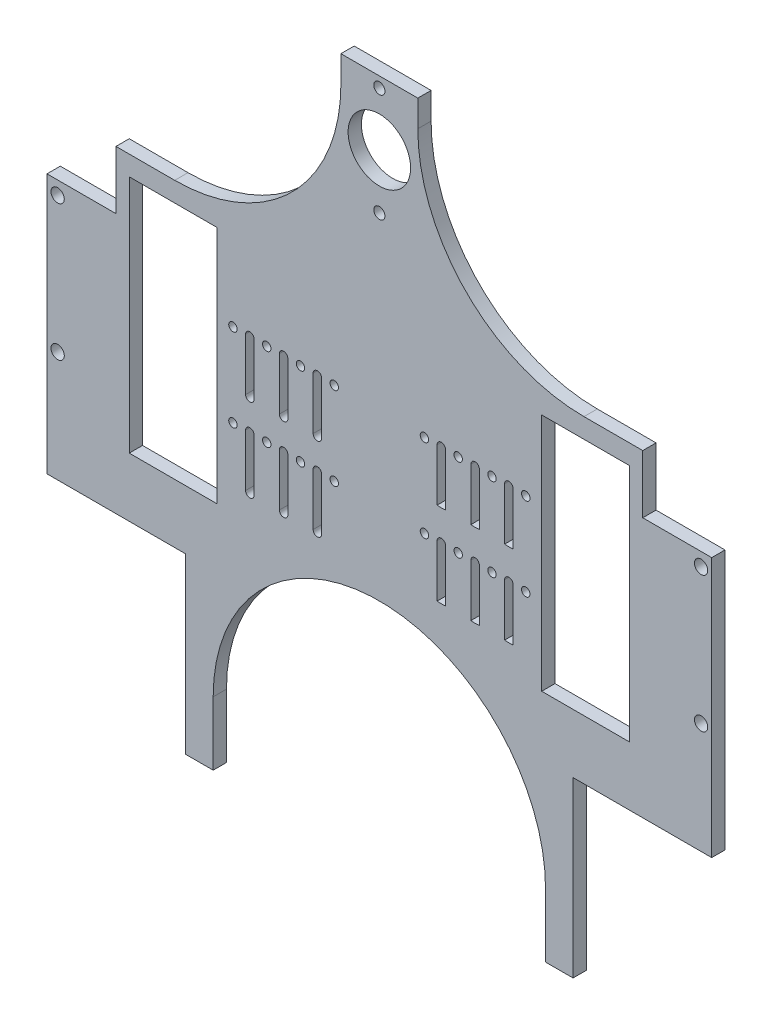
SolidWorks part; units mm, degrees
ref_plane "Front Plane" through (0, 0, 0) normal (0, 0, 1) x (1, 0, 0)
ref_plane "Top Plane" through (0, 0, 0) normal (0, 1, 0) x (1, 0, 0)
ref_plane "Right Plane" through (0, 0, 0) normal (1, 0, 0) x (0, 0, -1)
sketch "Sketch1" plane through (0, 0, 0) normal (0, 0, 1) x (1, 0, 0)
  line L0 (125, 0) -> (125, -340.4) construction
  line L1 (0, 0) -> (250, 0)
  line L2 (0, 0) -> (0, -340.4)
  line L3 (0, -340.4) -> (250, -340.4)
  line L4 (250, 0) -> (250, -340.4)
  line L9 (186.06, -79.9) -> (219.06, -79.9)
  line L10 (186.06, -79.9) -> (186.06, -169.9)
  line L11 (186.06, -169.9) -> (219.06, -169.9)
  line L12 (219.06, -79.9) -> (219.06, -169.9)
  line L13 (180.06, -124.9) -> (228.95, -124.9) construction
  line L14 (141.96, -109.275) -> (148.31, -109.275) construction
  line L21 (180.06, -124.9) -> (219.06, -124.9) construction
  line L25 (141.96, -140.525) -> (148.31, -140.525) construction
  line L32 (148.31, -109.275) -> (148.31, -114.275) construction
  line L33 (146.7225, -109.275) -> (146.7225, -128.9546)
  line L34 (149.8975, -109.275) -> (149.8975, -128.9546)
  line L35 (161.01, -109.275) -> (161.01, -114.275) construction
  line L36 (159.42, -109.275) -> (159.42, -128.9546)
  line L37 (162.6, -109.275) -> (162.6, -128.9546)
  line L38 (173.71, -109.275) -> (173.71, -114.275) construction
  line L39 (172.12, -109.275) -> (172.12, -128.9546)
  line L40 (175.3, -109.275) -> (175.3, -128.9546)
  line L41 (148.31, -109.275) -> (154.66, -109.275) construction
  line L42 (154.66, -109.275) -> (161.01, -109.275) construction
  line L43 (161.01, -109.275) -> (167.36, -109.275) construction
  line L44 (167.36, -109.275) -> (173.71, -109.275) construction
  line L45 (173.71, -109.275) -> (180.06, -109.275) construction
  line L48 (228.95, -124.9) -> (148.31, -124.9) construction
  line L52 (205.06, -79.9) -> (205.06, -169.9) construction
  line L53 (195.06, -79.9) -> (215.06, -79.9) construction
  line L54 (195.06, -79.9) -> (195.06, -169.9) construction
  line L55 (195.06, -169.9) -> (215.06, -169.9) construction
  line L56 (215.06, -79.9) -> (215.06, -169.9) construction
  line L62 (148.31, -140.525) -> (148.31, -145.525) construction
  line L65 (146.7225, -140.525) -> (146.7225, -160.2046)
  line L68 (149.8975, -140.525) -> (149.8975, -160.2046)
  line L71 (161.01, -140.525) -> (161.01, -145.525) construction
  line L78 (159.42, -140.525) -> (159.42, -160.2046)
  line L79 (162.6, -140.525) -> (162.6, -160.2046)
  line L80 (173.71, -140.525) -> (173.71, -145.525) construction
  line L83 (172.12, -140.525) -> (172.12, -160.2046)
  line L87 (148.31, -124.9) -> (101.69, -124.9) construction
  line L90 (180.06, -109.275) -> (180.06, -140.525) construction
  line L93 (148.31, -109.275) -> (148.31, -124.9) construction
  line L102 (246, -99.4) -> (246, -150.4) construction
  line L103 (219.06, -124.9) -> (246, -124.9) construction
  line L105 (175.3, -140.525) -> (175.3, -160.2046)
  line L106 (148.31, -140.525) -> (154.66, -140.525) construction
  line L107 (154.66, -140.525) -> (161.01, -140.525) construction
  line L108 (161.01, -140.525) -> (167.36, -140.525) construction
  line L109 (167.36, -140.525) -> (173.71, -140.525) construction
  line L110 (173.71, -140.525) -> (180.06, -140.525) construction
  line L111 (101.69, -109.275) -> (101.69, -128.9546) construction
  line L112 (103.2775, -109.275) -> (103.2775, -128.9546)
  line L113 (100.1025, -109.275) -> (100.1025, -128.9546)
  line L114 (88.99, -109.275) -> (88.99, -128.9546) construction
  line L115 (90.58, -109.275) -> (90.58, -128.9546)
  line L116 (87.4, -109.275) -> (87.4, -128.9546)
  line L117 (76.29, -109.275) -> (76.29, -128.9546) construction
  line L118 (77.88, -109.275) -> (77.88, -128.9546)
  line L119 (74.7, -109.275) -> (74.7, -128.9546)
  line L120 (101.69, -140.525) -> (101.69, -160.2046) construction
  line L121 (103.2775, -140.525) -> (103.2775, -160.2046)
  line L122 (100.1025, -140.525) -> (100.1025, -160.2046)
  line L123 (88.99, -140.525) -> (88.99, -160.2046) construction
  line L124 (90.58, -140.525) -> (90.58, -160.2046)
  line L125 (87.4, -140.525) -> (87.4, -160.2046)
  line L126 (76.29, -140.525) -> (76.29, -160.2046) construction
  line L127 (77.88, -140.525) -> (77.88, -160.2046)
  line L128 (74.7, -140.525) -> (74.7, -160.2046)
  line L129 (76.29, -140.525) -> (69.94, -140.525) construction
  line L130 (82.64, -140.525) -> (76.29, -140.525) construction
  line L131 (88.99, -140.525) -> (82.64, -140.525) construction
  line L132 (95.34, -140.525) -> (88.99, -140.525) construction
  line L133 (101.69, -140.525) -> (95.34, -140.525) construction
  line L134 (30.94, -124.9) -> (4, -124.9) construction
  line L135 (4, -99.4) -> (4, -150.4) construction
  line L136 (101.69, -109.275) -> (101.69, -124.9) construction
  line L137 (69.94, -109.275) -> (69.94, -140.525) construction
  line L139 (34.94, -79.9) -> (34.94, -169.9) construction
  line L140 (54.94, -169.9) -> (34.94, -169.9) construction
  line L141 (54.94, -79.9) -> (54.94, -169.9) construction
  line L142 (54.94, -79.9) -> (34.94, -79.9) construction
  line L143 (44.94, -79.9) -> (44.94, -169.9) construction
  line L144 (21.05, -124.9) -> (101.69, -124.9) construction
  line L145 (76.29, -109.275) -> (69.94, -109.275) construction
  line L146 (82.64, -109.275) -> (76.29, -109.275) construction
  line L147 (88.99, -109.275) -> (82.64, -109.275) construction
  line L148 (95.34, -109.275) -> (88.99, -109.275) construction
  line L149 (101.69, -109.275) -> (95.34, -109.275) construction
  line L150 (108.04, -140.525) -> (101.69, -140.525) construction
  line L151 (69.94, -124.9) -> (30.94, -124.9) construction
  line L152 (108.04, -109.275) -> (101.69, -109.275) construction
  line L153 (69.94, -124.9) -> (21.05, -124.9) construction
  line L154 (30.94, -79.9) -> (30.94, -169.9)
  line L155 (63.94, -169.9) -> (30.94, -169.9)
  line L156 (63.94, -79.9) -> (63.94, -169.9)
  line L157 (63.94, -79.9) -> (30.94, -79.9)
  arc A6 (175.3, -109.275) -> (172.12, -109.275) centre (173.71, -109.275) cw construction
  arc A7 (172.12, -109.275) -> (175.3, -109.275) centre (173.71, -109.275) cw
  arc A10 (159.42, -109.275) -> (162.6, -109.275) centre (161.01, -109.275) cw
  arc A11 (162.6, -109.275) -> (159.42, -109.275) centre (161.01, -109.275) cw construction
  arc A14 (146.7225, -109.275) -> (149.8975, -109.275) centre (148.31, -109.275) cw
  arc A15 (149.8975, -109.275) -> (146.7225, -109.275) centre (148.31, -109.275) cw construction
  arc A39 (149.8975, -128.9546) -> (146.7225, -128.9546) centre (148.31, -114.275) cw
  circle A40 centre (125, -44.64) radius 2.1
  arc A41 (162.6, -128.9546) -> (159.42, -128.9546) centre (161.01, -114.275) cw
  circle A42 centre (125, -4) radius 2.1
  arc A43 (175.3, -128.9546) -> (172.12, -128.9546) centre (173.71, -114.275) cw
  circle A84 centre (246, -99.4) radius 2.5
  circle A85 centre (246, -150.4) radius 2.5
  circle A179 centre (180.06, -109.275) radius 1.59
  arc A182 (175.3, -140.525) -> (172.12, -140.525) centre (173.71, -140.525) cw construction
  arc A183 (172.12, -140.525) -> (175.3, -140.525) centre (173.71, -140.525) cw
  arc A184 (159.42, -140.525) -> (162.6, -140.525) centre (161.01, -140.525) cw
  arc A185 (162.6, -140.525) -> (159.42, -140.525) centre (161.01, -140.525) cw construction
  arc A188 (146.7225, -140.525) -> (149.8975, -140.525) centre (148.31, -140.525) cw
  arc A189 (149.8975, -140.525) -> (146.7225, -140.525) centre (148.31, -140.525) cw construction
  arc A193 (149.8975, -160.2046) -> (146.7225, -160.2046) centre (148.31, -145.525) cw
  arc A195 (162.6, -160.2046) -> (159.42, -160.2046) centre (161.01, -145.525) cw
  arc A197 (175.3, -160.2046) -> (172.12, -160.2046) centre (173.71, -145.525) cw
  circle A198 centre (180.06, -140.525) radius 1.59
  circle A199 centre (125, -24.14) radius 11.75
  circle A200 centre (141.96, -109.275) radius 1.59
  circle A201 centre (154.66, -109.275) radius 1.59
  circle A202 centre (167.36, -109.275) radius 1.59
  circle A203 centre (141.96, -140.525) radius 1.59
  circle A204 centre (154.66, -140.525) radius 1.59
  circle A205 centre (167.36, -140.525) radius 1.59
  arc A206 (103.2775, -109.275) -> (100.1025, -109.275) centre (101.69, -109.275) ccw
  arc A207 (100.1025, -128.9546) -> (103.2775, -128.9546) centre (101.69, -128.9546) ccw
  arc A208 (90.58, -109.275) -> (87.4, -109.275) centre (88.99, -109.275) ccw
  arc A209 (87.4, -128.9546) -> (90.58, -128.9546) centre (88.99, -128.9546) ccw
  arc A210 (77.88, -109.275) -> (74.7, -109.275) centre (76.29, -109.275) ccw
  arc A211 (74.7, -128.9546) -> (77.88, -128.9546) centre (76.29, -128.9546) ccw
  arc A212 (103.2775, -140.525) -> (100.1025, -140.525) centre (101.69, -140.525) ccw
  arc A213 (100.1025, -160.2046) -> (103.2775, -160.2046) centre (101.69, -160.2046) ccw
  arc A214 (90.58, -140.525) -> (87.4, -140.525) centre (88.99, -140.525) ccw
  arc A215 (87.4, -160.2046) -> (90.58, -160.2046) centre (88.99, -160.2046) ccw
  arc A216 (77.88, -140.525) -> (74.7, -140.525) centre (76.29, -140.525) ccw
  arc A217 (74.7, -160.2046) -> (77.88, -160.2046) centre (76.29, -160.2046) ccw
  arc A218 (100.1025, -140.525) -> (103.2775, -140.525) centre (101.69, -140.525) ccw construction
  arc A219 (87.4, -140.525) -> (90.58, -140.525) centre (88.99, -140.525) ccw construction
  arc A220 (74.7, -140.525) -> (77.88, -140.525) centre (76.29, -140.525) ccw construction
  arc A221 (100.1025, -109.275) -> (103.2775, -109.275) centre (101.69, -109.275) ccw construction
  arc A222 (87.4, -109.275) -> (90.58, -109.275) centre (88.99, -109.275) ccw construction
  arc A223 (74.7, -109.275) -> (77.88, -109.275) centre (76.29, -109.275) ccw construction
  circle A224 centre (82.64, -140.525) radius 1.59
  circle A225 centre (95.34, -140.525) radius 1.59
  circle A226 centre (108.04, -140.525) radius 1.59
  circle A227 centre (82.64, -109.275) radius 1.59
  circle A228 centre (95.34, -109.275) radius 1.59
  circle A229 centre (108.04, -109.275) radius 1.59
  circle A230 centre (69.94, -140.525) radius 1.59
  circle A234 centre (69.94, -109.275) radius 1.59
  circle A236 centre (4, -150.4) radius 2.5
  circle A237 centre (4, -99.4) radius 2.5
  point P64 (148.31, -124.9)
  point P65 (101.69, -119.1148)
  point P69 (228.95, -124.9)
  point P71 (221, -87.34)
  point P76 (233.7, -87.34)
  point P78 (221, -54.5)
  point P82 (233.7, -54.5)
  point P86 (246.4, -54.5)
  point P93 (180.06, -124.9)
  point P97 (246.4, -87.34)
  point P104 (88.99, -119.1148)
  point P111 (76.29, -119.1148)
  point P119 (101.69, -150.3648)
  point P126 (88.99, -150.3648)
  point P133 (76.29, -150.3648)
  point P155 (125, -76.5574)
  point P166 (125, -124.9)
  point P183 (125, -76.5574)
  point P199 (69.94, -124.9)
  point P200 (21.05, -124.9)
  point P201 (101.69, -124.9)
  dimension "D5" = 20
  dimension "D10" = 5
  dimension "D12" = 3.18
  dimension "D15" = 5
  dimension "D16" = 5
  dimension "D19" = 3.18
  dimension "D20" = 1.5875
  dimension "D21" = 3.18
  dimension "D22" = 1.59
  dimension "D23" = 3.18
  dimension "D24" = 1.59
  dimension "D25" = 3.18
  dimension "D33" = 3.18
  dimension "D34" = 5
  dimension "D35" = 40.64
  dimension "D32" = 1.5875
  dimension "D36" = 1.59
  dimension "D37" = 3.18
  dimension "D39" = 1.59
  dimension "D47" = 3.18
  dimension "D49" = 23.5
  dimension "D53" = 4.2
  dimension "D54" = 4.2
  dimension "D1" = 250
  dimension "D2" = 340.4
  dimension "D3" = 4
  dimension "D4" = 90
  dimension "D6" = 90
  dimension "D7" = 9
  dimension "D8" = 6
  dimension "D9" = 5
  dimension "D11" = 6.35
  dimension "D13" = 6.35
  dimension "D14" = 90.06
  dimension "D17" = 25.5
  dimension "D18" = 4
  dimension "D26" = 5
  dimension "D27" = 6.35
  dimension "D28" = 6.35
  dimension "D29" = 6.35
  dimension "D30" = 6.35
  dimension "D31" = 6.35
  dimension "D40" = 5
  dimension "D41" = 6.35
  dimension "D42" = 6.35
  dimension "D43" = 6.35
  dimension "D44" = 6.35
  dimension "D45" = 6.35
  dimension "D46" = 5
  dimension "D48" = 31.25
  dimension "D52" = 20.5
  dimension "D55" = 4
extrude "Boss-Extrude1" add sketch "Sketch1" along normal blind 5
sketch "Sketch12" plane through (0, -340.4, 0) normal (0, -1, 0) x (1, 0, 0)
  line L0 (0, 0) -> (250, 0)
  line L1 (0, 0) -> (0, 5)
  line L2 (250, 0) -> (250, 5)
  line L3 (0, 5) -> (250, 5)
  line L5 (0, 5) -> (250, 5) construction
extrude "Cut-Extrude2" cut sketch "Sketch12" against normal blind 83
sketch "Sketch14" plane through (0, 0, 5) normal (0, 0, 1) x (1, 0, 0)
  line L0 (-135.3499, -257.4) -> (537.3728, -257.4) construction
  line L1 (250, -257.4) -> (0, -257.4) construction
sketch "Sketch11" plane through (0, 0, 5) normal (0, 0, 1) x (1, 0, 0)
  line L1 (0, 0) -> (0, -257.4) construction
  line L2 (250, -257.4) -> (250, 0) construction
  line L3 (0, -72.5) -> (250, -72.5) construction
  line L6 (-135.3499, -257.4) -> (537.3728, -257.4) construction
  line L8 (250, 0) -> (0, 0) construction
  line L9 (187.5, 0) -> (187.5, -298.6981) construction
  line L10 (245, 0) -> (245, -350.4) construction
  line L11 (185, 0) -> (185, -298.6981) construction
  line L19 (0, -79.9) -> (250, -79.9) construction
  line L20 (0, -165.0962) -> (-19.47, -165.0962) construction
  line L22 (125, 0) -> (125, -350.4) construction
  line L23 (63.94, -79.9) -> (30.94, -79.9) construction
  line L27 (162.6, -128.9546) -> (162.6, -109.275) construction
  line L30 (74.7, -109.275) -> (74.7, -128.9546) construction
  line L31 (5, -350.4) -> (5, 0) construction
  line L33 (65, -298.6981) -> (65, 0) construction
  line L34 (250, -257.4) -> (0, -257.4) construction
  line L35 (62.5, 0) -> (62.5, -298.6981) construction
  line L36 (250, -165.0962) -> (269.47, -165.0962) construction
  line L37 (250, -165.0962) -> (250, -83.981) construction
  line L38 (269.47, -165.0962) -> (269.47, -83.981) construction
  line L39 (250, -83.981) -> (269.47, -83.981) construction
  line L40 (269.47, -162.9) -> (269.47, -86.9) construction
  line L41 (0, -165.0962) -> (0, -83.981) construction
  line L42 (-19.47, -165.0962) -> (-19.47, -83.981) construction
  line L43 (0, -83.981) -> (-19.47, -83.981) construction
  line L44 (0, -170.9981) -> (250, -170.9981) construction
  line L45 (0, 0) -> (0, -257.4) construction
  line L46 (250, -257.4) -> (250, 0) construction
  line L48 (65, -298.6981) -> (62.5, -298.6981) construction
  line L49 (182.5, -298.6981) -> (67.5, -298.6981) construction
  line L50 (185, -298.6981) -> (187.5, -298.6981) construction
  line L51 (0, 0) -> (250, 0) construction
  line L52 (250, 0) -> (265.87, -70.4) construction
  line L54 (265.87, -70.4) -> (269.47, -83.981) construction
  line L55 (269.47, -83.981) -> (269.47, -165.0962) construction
  line L56 (269.47, -165.0962) -> (266, -192.1922) construction
  line L60 (250, -257.4) -> (182.5, -298.6981) construction
  line L61 (182.5, -298.6981) -> (67.5, -298.6981) construction
  line L62 (67.5, -298.6981) -> (0, -257.4) construction
  line L63 (0, -257.4) -> (-19.47, -165.0962) construction
  line L64 (-19.47, -165.0962) -> (-19.47, -83.981) construction
  line L65 (-19.47, -83.981) -> (-15.87, -70.4) construction
  line L66 (-15.87, -70.4) -> (0, 0) construction
  line L67 (266, -192.1922) -> (250, -257.4) construction
  circle A11 centre (125, -233.4981) radius 60 construction
  circle A12 centre (125, -233.4981) radius 62.5 construction
  circle A13 centre (209.62, -96.7828) radius 24.62 construction
  circle A14 centre (48.0382, -10) radius 62.5 construction
  circle A17 centre (43.8621, -92.5792) radius 20.1848 construction
  circle A18 centre (201.9618, -10) radius 62.5 construction
  circle A19 centre (212.12, -227.4) radius 24.62 construction
  circle A20 centre (37.88, -227.4) radius 24.62 construction
  circle A21 centre (125, -24.14) radius 11.75 construction
  circle A22 centre (125, -108.4981) radius 62.5 construction
  circle A23 centre (48.0382, -10) radius 10 construction
  circle A24 centre (201.9618, -10) radius 10 construction
  dimension "D4" = 5
  dimension "D5" = 125
  dimension "D3" = 120
  dimension "D9" = 7.4
  dimension "D10" = 125
  dimension "D11" = 2.5
  dimension "D12" = 2.5
  dimension "D13" = 78.25
  dimension "D14" = 20
  dimension "D16" = 49.24
  dimension "D8" = 49.24
  dimension "D15" = 20
  dimension "D6" = 125
  dimension "D2" = 30
  dimension "D17" = 78.25
  dimension "D18" = 125
  dimension "D7" = 5
sketch "Sketch13" plane through (0, 0, 5) normal (0, 0, 1) x (1, 0, 0)
  line L0 (25.94, -72.5) -> (201.9618, -72.5) construction
  line L1 (48.0382, -72.5) -> (25.94, -72.5)
  line L5 (250, 0) -> (250, -94.4)
  line L6 (0, -79.9) -> (36, -79.9) construction
  line L7 (63.94, -79.9) -> (30.94, -79.9) construction
  line L8 (0, 0) -> (0, -257.4) construction
  line L9 (0, -72.5) -> (250, -72.5) construction
  line L10 (250, -257.4) -> (250, 0) construction
  line L12 (62.5, -233.4981) -> (62.5, -350.4)
  line L14 (62.5, -350.4) -> (187.5, -350.4)
  line L15 (187.5, -233.4981) -> (187.5, -350.4)
  line L16 (250, 0) -> (140.267, 0)
  line L17 (62.5, 0) -> (62.5, -298.6981) construction
  line L20 (109.733, 0) -> (0, 0)
  line L21 (250, 0) -> (0, 0) construction
  line L31 (224.06, -72.5) -> (224.06, -94.4)
  line L32 (250, -94.4) -> (224.06, -94.4)
  line L33 (201.9618, -72.5) -> (224.06, -72.5)
  line L35 (125, 0) -> (125, -350.4) construction
  line L36 (0, -94.4) -> (25.94, -94.4)
  line L37 (25.94, -72.5) -> (25.94, -94.4)
  line L38 (0, 0) -> (0, -94.4)
  line L41 (219.06, -169.9) -> (219.06, -79.9) construction
  arc A0 (48.0382, -72.5) -> (109.733, 0) centre (48.0382, -10) ccw
  arc A1 (140.267, 0) -> (201.9618, -72.5) centre (201.9618, -10) ccw
  circle A2 centre (48.0382, -10) radius 65 construction
  arc A3 (250, -53.7874) -> (224.06, -71.1283) centre (201.9618, -10) ccw construction
  arc A5 (187.5, -233.4981) -> (62.5, -233.4981) centre (125, -233.4981) ccw
  circle A6 centre (201.9618, -10) radius 62.5 construction
  circle A7 centre (48.0382, -10) radius 62.5 construction
  circle A9 centre (125, -233.4981) radius 62.5 construction
  circle A10 centre (246, -99.4) radius 2.5 construction
  dimension "D2" = 130
  dimension "D3" = 62.5
  dimension "D4" = 130
  dimension "D5" = 62.5
  dimension "D1" = 5
  dimension "D6" = 5
extrude "Cut-Extrude3" cut sketch "Sketch13" against normal through all
sketch "Sketch15" plane through (0, 0, 5) normal (0, 0, 1) x (1, 0, 0)
  line L0 (139.4618, 13.1038) -> (139.4618, -10) construction
  line L1 (110.5382, 16.9922) -> (110.5382, -10) construction
  line L2 (140.267, 0) -> (109.733, 0) construction
  line L3 (110.5382, -10) -> (110.5382, 0)
  line L4 (110.5382, -10) -> (80.4559, -10)
  line L5 (110.5382, 0) -> (80.4559, 0)
  line L6 (80.4559, -10) -> (80.4559, 0)
  line L7 (139.4618, -10) -> (139.4618, 0)
  line L8 (139.4618, -10) -> (165.496, -10)
  line L9 (139.4618, 0) -> (165.496, 0)
  line L10 (165.496, -10) -> (165.496, 0)
  arc A0 (48.0382, -72.5) -> (109.733, 0) centre (48.0382, -10) ccw construction
  arc A1 (140.267, 0) -> (201.9618, -72.5) centre (201.9618, -10) ccw construction
extrude "Cut-Extrude4" cut sketch "Sketch15" against normal blind 10
sketch "Sketch17" plane through (0, 0, 5) normal (0, 0, 1) x (1, 0, 0)
  line L4 (250, -192.1215) -> (197.8516, -192.1215)
  line L5 (125, -350.4) -> (125, 0) construction
  line L11 (250, -192.1215) -> (250, -258.9015)
  line L24 (197.8516, -192.1215) -> (197.8516, -258.9015)
  line L25 (250, -258.9015) -> (197.8516, -258.9015)
  line L26 (250, -257.4) -> (250, -94.4) construction
  line L27 (0, -258.9015) -> (52.1484, -258.9015)
  line L28 (52.1484, -192.1215) -> (52.1484, -258.9015)
  line L29 (0, -192.1215) -> (0, -258.9015)
  line L30 (0, -192.1215) -> (52.1484, -192.1215)
extrude "Cut-Extrude5" cut sketch "Sketch17" against normal blind 10
sketch "Sketch16" plane through (0, 0, 5) normal (0, 0, 1) x (1, 0, 0)
  line L0 (125, 0) -> (125, -350.4) construction
  line L1 (43.8621, -92.5792) -> (82.2859, -19.3646) construction
  line L2 (139.4618, 0) -> (110.5382, 0) construction
  circle A0 centre (82.2859, -19.3646) radius 62.5 construction
  circle A1 centre (43.8621, -92.5792) radius 20.1848 construction
  circle A3 centre (125, -108.4981) radius 62.5 construction
  circle A5 centre (125, -108.4981) radius 62.5 construction
  circle A6 centre (43.8621, -92.5792) radius 20.1848 construction
  circle A7 centre (206.1379, -92.5792) radius 20.1848 construction
  circle A8 centre (167.7141, -19.3646) radius 62.5 construction
  dimension "D1" = 125
sketch "Sketch18" plane through (0, 0, 5) normal (0, 0, 1) x (1, 0, 0)
  line L0 (125, 3.6737) -> (125, -226.8138) construction
  line L1 (0, -94.4) -> (0, -192.1215) construction
  line L2 (250, -192.1215) -> (250, -94.4) construction
  line L3 (83.9199, -192.0021) -> (158.7429, -192.0021) construction
  line L4 (0, -169.7699) -> (250, -169.7699)
  line L5 (0, -169.7699) -> (0, -205.7551)
  line L6 (250, -169.7699) -> (250, -205.7551)
  line L7 (0, -205.7551) -> (250, -205.7551)
  circle A0 centre (125, -192.0021) radius 11.75
  circle A1 centre (125, -24.14) radius 11.75 construction
  circle A2 centre (145.14, -192.0021) radius 2.1
  circle A3 centre (104.86, -192.0021) radius 2.1
  point P12 (125, -24.14)
  point P16 (125, -4)
  dimension "D1" = 23.5
  dimension "D3" = 4.2
  dimension "D4" = 4.2
  dimension "D2" = 20.14
  dimension "20,14" = 20.14
  dimension "D5" = 13.753
